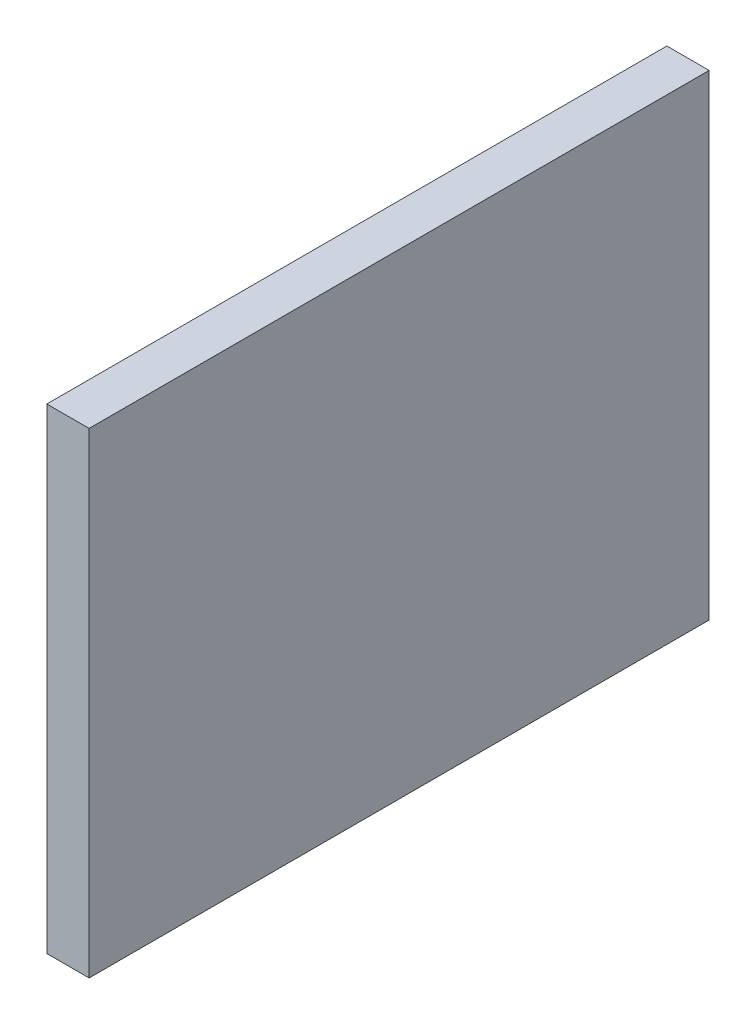
SolidWorks part; units mm, degrees
ref_plane "Front Plane" through (0, 0, 0) normal (0, 0, 1) x (1, 0, 0)
ref_plane "Top Plane" through (0, 0, 0) normal (0, 1, 0) x (1, 0, 0)
ref_plane "Right Plane" through (0, 0, 0) normal (1, 0, 0) x (0, 0, -1)
sketch "Sketch1" plane through (0, 0, 0) normal (1, 0, 0) x (0, 0, -1)
  line L1 (-2.9616, -56.7137) -> (41.0384, -56.7137)
  line L2 (-2.9616, -56.7137) -> (-2.9616, -22.9377)
  line L3 (-2.9616, -22.9377) -> (41.0384, -22.9377)
  line L4 (41.0384, -56.7137) -> (41.0384, -22.9377)
  point P0 (0, 0)
  point P6 (-51.9616, -22.9377)
  point P7 (0, 0)
extrude "Boss-Extrude1" add sketch "Sketch1" along normal blind 3
